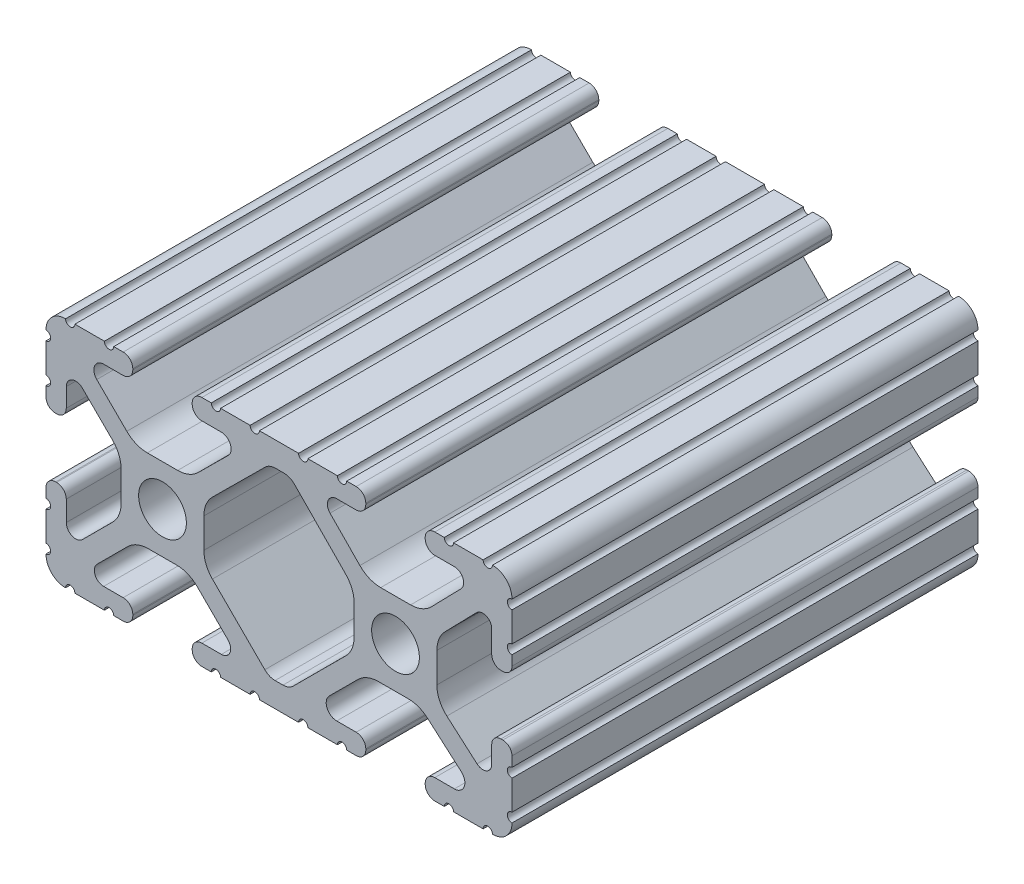
SolidWorks part; units mm, degrees
ref_plane "Front Plane" through (0, 0, 0) normal (0, 0, 1) x (1, 0, 0)
ref_plane "Top Plane" through (0, 0, 0) normal (0, 1, 0) x (1, 0, 0)
ref_plane "Right Plane" through (0, 0, 0) normal (1, 0, 0) x (0, 0, -1)
sketch "Sketch1" plane through (0, 0, 0) normal (0, 0, 1) x (1, 0, 0)
  line L0 (-7.2595, -3.8694) -> (-1.5457, -9.5728)
  line L1 (-8.1915, 1.6223) -> (-8.1915, -1.6223)
  line L2 (-1.504, 9.5765) -> (-7.252, 3.8768)
  line L3 (0.5515, 10.033) -> (-0.3952, 10.033)
  line L4 (7.2829, 3.8459) -> (1.6756, 9.5611)
  line L5 (8.1915, -1.6223) -> (8.1915, 1.6223)
  line L6 (1.5457, -9.5728) -> (7.2595, -3.8694)
  line L7 (-0.4332, -10.033) -> (0.4332, -10.033)
  line L8 (18.0171, 12.7) -> (16.9875, 12.7)
  line L9 (15.9385, 11.651) -> (15.9385, 11.5392)
  line L10 (16.9875, 10.4902) -> (19.1164, 10.4902)
  line L11 (19.8441, 8.7652) -> (16.619, 5.4551)
  line L12 (14.3449, 4.4958) -> (11.0833, 4.4958)
  line L13 (8.817, 5.4472) -> (5.5642, 8.7627)
  line L14 (6.2894, 10.4902) -> (8.4125, 10.4902)
  line L15 (9.4615, 11.5392) -> (9.4615, 11.651)
  line L16 (8.4125, 12.7) -> (7.3829, 12.7)
  line L17 (6.3669, 12.7) -> (3.1496, 12.7)
  line L18 (2.1336, 12.7) -> (-2.1336, 12.7)
  line L19 (-3.1496, 12.7) -> (-6.3669, 12.7)
  line L20 (-7.3829, 12.7) -> (-8.4125, 12.7)
  line L21 (-9.4615, 11.651) -> (-9.4615, 11.5392)
  line L22 (-8.4125, 10.4902) -> (-6.2836, 10.4902)
  line L23 (-5.5326, 8.6661) -> (-8.81, 5.4163)
  line L24 (-11.0455, 4.4958) -> (-14.3545, 4.4958)
  line L25 (-16.59, 5.4163) -> (-19.8674, 8.6661)
  line L26 (-19.1164, 10.4902) -> (-16.9875, 10.4902)
  line L27 (-15.9385, 11.5392) -> (-15.9385, 11.651)
  line L28 (-16.9875, 12.7) -> (-18.0171, 12.7)
  line L29 (-19.0331, 12.7) -> (-22.2504, 12.7)
  line L30 (-25.4, 9.5504) -> (-25.4, 6.3331)
  line L31 (-25.4, 5.3171) -> (-25.4, 4.2375)
  line L32 (-24.401, 3.2385) -> (-24.2392, 3.2385)
  line L33 (-23.1902, 4.2875) -> (-23.1902, 6.3347)
  line L34 (-21.434, 7.0665) -> (-18.148, 3.8082)
  line L35 (-17.2085, 1.5536) -> (-17.2085, -1.6952)
  line L36 (-18.1405, -3.9423) -> (-21.4316, -7.2274)
  line L37 (-23.1902, -6.498) -> (-23.1902, -4.2875)
  line L38 (-24.2392, -3.2385) -> (-24.351, -3.2385)
  line L39 (-25.4, -4.2875) -> (-25.4, -5.3171)
  line L40 (-25.4, -6.3331) -> (-25.4, -9.5504)
  line L41 (-22.2504, -12.7) -> (-19.0331, -12.7)
  line L42 (-18.0171, -12.7) -> (-16.9875, -12.7)
  line L43 (-15.9384, -11.651) -> (-15.9384, -11.5392)
  line L44 (-16.9875, -10.4902) -> (-19.1164, -10.4902)
  line L45 (-19.8341, -8.7551) -> (-16.4966, -5.4237)
  line L46 (-14.2536, -4.4958) -> (-11.1464, -4.4958)
  line L47 (-8.9034, -5.4237) -> (-5.5659, -8.7551)
  line L48 (-6.2836, -10.4902) -> (-8.4125, -10.4902)
  line L49 (-9.4616, -11.5392) -> (-9.4616, -11.651)
  line L50 (-8.4125, -12.7) -> (-7.3829, -12.7)
  line L51 (-6.3669, -12.7) -> (-3.1496, -12.7)
  line L52 (-2.1336, -12.7) -> (2.1336, -12.7)
  line L53 (3.1496, -12.7) -> (6.3669, -12.7)
  line L54 (7.3829, -12.7) -> (8.4125, -12.7)
  line L55 (9.4616, -11.651) -> (9.4616, -11.5392)
  line L56 (8.4125, -10.4902) -> (6.2894, -10.4902)
  line L57 (5.4807, -8.5353) -> (8.5979, -5.4237)
  line L58 (10.8409, -4.4958) -> (14.1026, -4.4958)
  line L59 (16.1879, -5.2766) -> (19.8682, -8.4822)
  line L60 (19.1164, -10.4902) -> (16.9875, -10.4902)
  line L61 (15.9384, -11.5392) -> (15.9384, -11.651)
  line L62 (16.9875, -12.7) -> (18.0171, -12.7)
  line L63 (19.0331, -12.7) -> (22.2504, -12.7)
  line L64 (25.4, -9.5504) -> (25.4, -6.3331)
  line L65 (25.4, -5.3171) -> (25.4, -4.2375)
  line L66 (24.401, -3.2385) -> (24.1892, -3.2385)
  line L67 (23.1902, -4.2375) -> (23.1902, -6.1559)
  line L68 (21.584, -6.8869) -> (18.2982, -4.025)
  line L69 (17.2085, -1.6308) -> (17.2085, 1.6308)
  line L70 (18.1094, 3.8465) -> (21.5263, 7.3534)
  line L71 (23.1902, 6.6769) -> (23.1902, 4.2375)
  line L72 (24.1892, 3.2385) -> (24.401, 3.2385)
  line L73 (25.4, 4.2375) -> (25.4, 5.3171)
  line L74 (25.4, 6.3332) -> (25.4, 9.5504)
  line L75 (22.2504, 12.7) -> (19.0331, 12.7)
  circle A0 centre (-12.7, 0) radius 2.6035
  circle A1 centre (12.7, 0) radius 2.6035
  arc A2 (-1.5457, -9.5728) -> (-0.4332, -10.033) centre (-0.4332, -8.4582) ccw
  arc A3 (-8.1915, -1.6223) -> (-7.2595, -3.8694) centre (-5.0165, -1.6223) ccw
  arc A4 (-7.252, 3.8768) -> (-8.1915, 1.6223) centre (-5.0165, 1.6223) ccw
  arc A5 (-0.3952, 10.033) -> (-1.504, 9.5765) centre (-0.3952, 8.4582) ccw
  arc A6 (1.6756, 9.5611) -> (0.5515, 10.033) centre (0.5515, 8.4582) ccw
  arc A7 (8.1915, 1.6223) -> (7.2829, 3.8459) centre (5.0165, 1.6223) ccw
  arc A8 (7.2595, -3.8694) -> (8.1915, -1.6223) centre (5.0165, -1.6223) ccw
  arc A9 (0.4332, -10.033) -> (1.5457, -9.5728) centre (0.4332, -8.4582) ccw
  arc A10 (18.0171, 12.7) -> (19.0331, 12.7) centre (18.5251, 12.7) ccw
  arc A11 (16.9875, 12.7) -> (15.9385, 11.651) centre (16.9875, 11.651) ccw
  arc A12 (15.9385, 11.5392) -> (16.9875, 10.4902) centre (16.9875, 11.5392) ccw
  arc A13 (19.8441, 8.7652) -> (19.1164, 10.4902) centre (19.1164, 9.4742) ccw
  arc A14 (14.3449, 4.4958) -> (16.619, 5.4551) centre (14.3449, 7.6708) ccw
  arc A15 (8.817, 5.4472) -> (11.0833, 4.4958) centre (11.0833, 7.6708) ccw
  arc A16 (6.2894, 10.4902) -> (5.5642, 8.7627) centre (6.2894, 9.4742) ccw
  arc A17 (8.4125, 10.4902) -> (9.4615, 11.5392) centre (8.4125, 11.5392) ccw
  arc A18 (9.4615, 11.651) -> (8.4125, 12.7) centre (8.4125, 11.651) ccw
  arc A19 (6.3669, 12.7) -> (7.3829, 12.7) centre (6.8749, 12.7) ccw
  arc A20 (2.1336, 12.7) -> (3.1496, 12.7) centre (2.6416, 12.7) ccw
  arc A21 (-3.1496, 12.7) -> (-2.1336, 12.7) centre (-2.6416, 12.7) ccw
  arc A22 (-7.3829, 12.7) -> (-6.3669, 12.7) centre (-6.8749, 12.7) ccw
  arc A23 (-8.4125, 12.7) -> (-9.4615, 11.651) centre (-8.4125, 11.651) ccw
  arc A24 (-9.4615, 11.5392) -> (-8.4125, 10.4902) centre (-8.4125, 11.5392) ccw
  arc A25 (-5.5326, 8.6661) -> (-6.2836, 10.4902) centre (-6.2836, 9.4235) ccw
  arc A26 (-11.0455, 4.4958) -> (-8.81, 5.4163) centre (-11.0455, 7.6708) ccw
  arc A27 (-16.59, 5.4163) -> (-14.3545, 4.4958) centre (-14.3545, 7.6708) ccw
  arc A28 (-19.1164, 10.4902) -> (-19.8674, 8.6661) centre (-19.1164, 9.4235) ccw
  arc A29 (-16.9875, 10.4902) -> (-15.9385, 11.5392) centre (-16.9875, 11.5392) ccw
  arc A30 (-15.9385, 11.651) -> (-16.9875, 12.7) centre (-16.9875, 11.651) ccw
  arc A31 (-19.0331, 12.7) -> (-18.0171, 12.7) centre (-18.5251, 12.7) ccw
  arc A32 (-23.2664, 12.6998) -> (-22.2504, 12.7) centre (-22.7584, 12.7) ccw
  arc A33 (-23.2664, 12.6998) -> (-25.3998, 10.5664) centre (-23.2918, 10.5918) ccw
  arc A34 (-25.4, 9.5504) -> (-25.3998, 10.5664) centre (-25.4, 10.0584) ccw
  arc A35 (-25.4, 5.3171) -> (-25.4, 6.3331) centre (-25.4, 5.8251) ccw
  arc A36 (-25.4, 4.2375) -> (-24.401, 3.2385) centre (-24.401, 4.2375) ccw
  arc A37 (-24.2392, 3.2385) -> (-23.1902, 4.2875) centre (-24.2392, 4.2875) ccw
  arc A38 (-21.434, 7.0665) -> (-23.1902, 6.3347) centre (-22.1596, 6.3347) ccw
  arc A39 (-17.2085, 1.5536) -> (-18.148, 3.8082) centre (-20.3835, 1.5536) ccw
  arc A40 (-18.1405, -3.9423) -> (-17.2085, -1.6952) centre (-20.3835, -1.6952) ccw
  arc A41 (-23.1902, -6.498) -> (-21.4316, -7.2274) centre (-22.1596, -6.498) ccw
  arc A42 (-23.1902, -4.2875) -> (-24.2392, -3.2385) centre (-24.2392, -4.2875) ccw
  arc A43 (-24.351, -3.2385) -> (-25.4, -4.2875) centre (-24.351, -4.2875) ccw
  arc A44 (-25.4, -6.3331) -> (-25.4, -5.3171) centre (-25.4, -5.8251) ccw
  arc A45 (-25.3998, -10.5664) -> (-25.4, -9.5504) centre (-25.4, -10.0584) ccw
  arc A46 (-25.3998, -10.5664) -> (-23.2664, -12.6998) centre (-23.2918, -10.5918) ccw
  arc A47 (-22.2504, -12.7) -> (-23.2664, -12.6998) centre (-22.7584, -12.7) ccw
  arc A48 (-18.0171, -12.7) -> (-19.0331, -12.7) centre (-18.5251, -12.7) ccw
  arc A49 (-16.9875, -12.7) -> (-15.9384, -11.651) centre (-16.9875, -11.651) ccw
  arc A50 (-15.9384, -11.5392) -> (-16.9875, -10.4902) centre (-16.9875, -11.5392) ccw
  arc A51 (-19.8341, -8.7551) -> (-19.1164, -10.4902) centre (-19.1164, -9.4742) ccw
  arc A52 (-14.2536, -4.4958) -> (-16.4966, -5.4237) centre (-14.2536, -7.6708) ccw
  arc A53 (-8.9034, -5.4237) -> (-11.1464, -4.4958) centre (-11.1464, -7.6708) ccw
  arc A54 (-6.2836, -10.4902) -> (-5.5659, -8.7551) centre (-6.2836, -9.4742) ccw
  arc A55 (-8.4125, -10.4902) -> (-9.4616, -11.5392) centre (-8.4125, -11.5392) ccw
  arc A56 (-9.4616, -11.651) -> (-8.4125, -12.7) centre (-8.4125, -11.651) ccw
  arc A57 (-6.3669, -12.7) -> (-7.3829, -12.7) centre (-6.8749, -12.7) ccw
  arc A58 (-2.1336, -12.7) -> (-3.1496, -12.7) centre (-2.6416, -12.7) ccw
  arc A59 (3.1496, -12.7) -> (2.1336, -12.7) centre (2.6416, -12.7) ccw
  arc A60 (7.3829, -12.7) -> (6.3669, -12.7) centre (6.8749, -12.7) ccw
  arc A61 (8.4125, -12.7) -> (9.4616, -11.651) centre (8.4125, -11.651) ccw
  arc A62 (9.4616, -11.5392) -> (8.4125, -10.4902) centre (8.4125, -11.5392) ccw
  arc A63 (5.4807, -8.5353) -> (6.2894, -10.4902) centre (6.2894, -9.3455) ccw
  arc A64 (10.8409, -4.4958) -> (8.5979, -5.4237) centre (10.8409, -7.6708) ccw
  arc A65 (16.1879, -5.2766) -> (14.1026, -4.4958) centre (14.1026, -7.6708) ccw
  arc A66 (19.1164, -10.4902) -> (19.8682, -8.4822) centre (19.1164, -9.3455) ccw
  arc A67 (16.9875, -10.4902) -> (15.9384, -11.5392) centre (16.9875, -11.5392) ccw
  arc A68 (15.9384, -11.651) -> (16.9875, -12.7) centre (16.9875, -11.651) ccw
  arc A69 (19.0331, -12.7) -> (18.0171, -12.7) centre (18.5251, -12.7) ccw
  arc A70 (23.2664, -12.6998) -> (22.2504, -12.7) centre (22.7584, -12.7) ccw
  arc A71 (23.2664, -12.6998) -> (25.3998, -10.5664) centre (23.2918, -10.5918) ccw
  arc A72 (25.4, -9.5504) -> (25.3998, -10.5664) centre (25.4, -10.0584) ccw
  arc A73 (25.4, -5.3171) -> (25.4, -6.3331) centre (25.4, -5.8251) ccw
  arc A74 (25.4, -4.2375) -> (24.401, -3.2385) centre (24.401, -4.2375) ccw
  arc A75 (24.1892, -3.2385) -> (23.1902, -4.2375) centre (24.1892, -4.2375) ccw
  arc A76 (21.584, -6.8869) -> (23.1902, -6.1559) centre (22.2207, -6.1559) ccw
  arc A77 (17.2085, -1.6308) -> (18.2982, -4.025) centre (20.3835, -1.6308) ccw
  arc A78 (18.1094, 3.8465) -> (17.2085, 1.6308) centre (20.3835, 1.6308) ccw
  arc A79 (23.1902, 6.6769) -> (21.5263, 7.3534) centre (22.2207, 6.6769) ccw
  arc A80 (23.1902, 4.2375) -> (24.1892, 3.2385) centre (24.1892, 4.2375) ccw
  arc A81 (24.401, 3.2385) -> (25.4, 4.2375) centre (24.401, 4.2375) ccw
  arc A82 (25.4, 6.3332) -> (25.4, 5.3171) centre (25.4, 5.8251) ccw
  arc A83 (25.3998, 10.5664) -> (25.4, 9.5504) centre (25.4, 10.0584) ccw
  arc A84 (25.3998, 10.5664) -> (23.2664, 12.6998) centre (23.2918, 10.5918) ccw
  arc A85 (22.2504, 12.7) -> (23.2664, 12.6998) centre (22.7584, 12.7) ccw
  point P248 (0, 10.033)
extrude "Boss-Extrude1" add sketch "Sketch1" along normal mid plane 50.8
